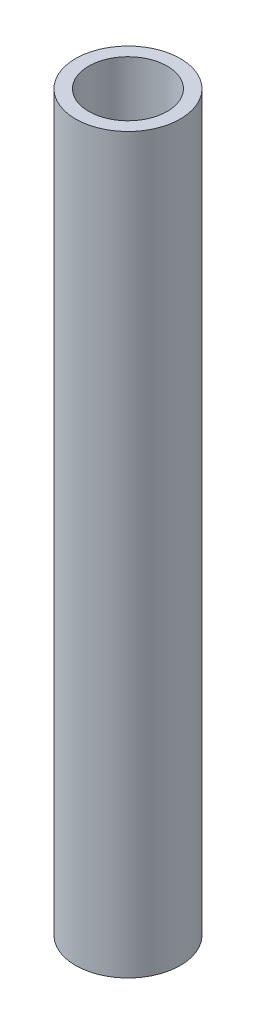
SolidWorks part; units mm, degrees
ref_plane "Front Plane" through (0, 0, 0) normal (0, 0, 1) x (1, 0, 0)
ref_plane "Top Plane" through (0, 0, 0) normal (0, 1, 0) x (1, 0, 0)
ref_plane "Right Plane" through (0, 0, 0) normal (1, 0, 0) x (0, 0, -1)
sketch "Sketch1" plane through (0, 0, 0) normal (0, 1, 0) x (1, 0, 0)
  circle A0 centre (0, 0) radius 12.7
  circle A1 centre (0, 0) radius 9.525
  dimension "D1" = 19.05
  dimension "D2" = 25.4
extrude "Boss-Extrude2" add sketch "Sketch1" along normal blind 177.8
